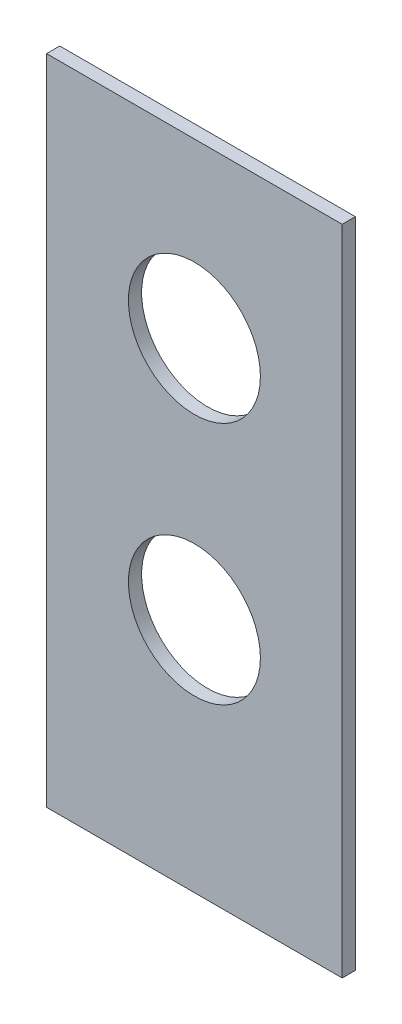
SolidWorks part; units mm, degrees
ref_plane "Front Plane" through (0, 0, 0) normal (0, 0, 1) x (1, 0, 0)
ref_plane "Top Plane" through (0, 0, 0) normal (0, 1, 0) x (1, 0, 0)
ref_plane "Right Plane" through (0, 0, 0) normal (1, 0, 0) x (0, 0, -1)
sketch "Sketch1" plane through (0, 0, 0) normal (0, 0, 1) x (1, 0, 0)
  line L1 (-28.4456, 62.8029) -> (28.4456, 62.8029)
  line L2 (-28.4456, 62.8029) -> (-28.4456, -62.8029)
  line L3 (-28.4456, -62.8029) -> (28.4456, -62.8029)
  line L4 (28.4456, 62.8029) -> (28.4456, -62.8029)
  line L5 (-28.4456, 62.8029) -> (28.4456, -62.8029) construction
  line L6 (-28.4456, -62.8029) -> (28.4456, 62.8029) construction
  point P0 (0, 0)
extrude "Boss-Extrude1" add sketch "Sketch1" along normal blind 2.54
sketch "Sketch2" plane through (0, 0, 2.54) normal (0, 0, 1) x (1, 0, 0)
  circle A0 centre (0, 29.58) radius 12.7
  circle A1 centre (0, -17.34) radius 12.7
extrude "Cut-Extrude1" cut sketch "Sketch2" against normal up to next
